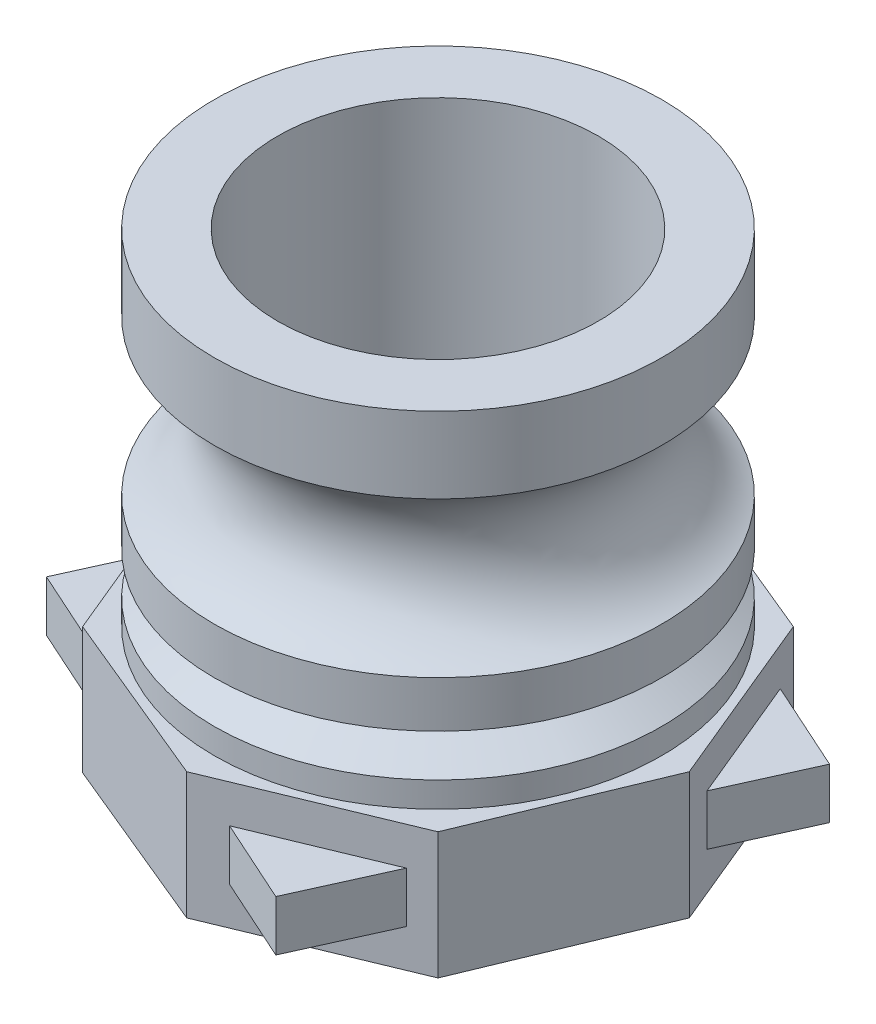
SolidWorks part; units mm, degrees
material "AISI 1020"
ref_plane "Front Plane" through (0, 0, 0) normal (0, 0, 1) x (1, 0, 0)
ref_plane "Top Plane" through (0, 0, 0) normal (0, 1, 0) x (1, 0, 0)
ref_plane "Right Plane" through (0, 0, 0) normal (1, 0, 0) x (0, 0, -1)
sketch "Sketch1" plane through (0, 0, 0) normal (0, 1, 0) x (1, 0, 0)
  line L1 (21.0476, 21.0476) -> (0, 29.7658)
  line L2 (0, 29.7658) -> (-21.0476, 21.0476)
  line L3 (-21.0476, 21.0476) -> (-29.7658, 0)
  line L4 (-29.7658, 0) -> (-21.0476, -21.0476)
  line L5 (-21.0476, -21.0476) -> (0, -29.7658)
  line L6 (0, -29.7658) -> (21.0476, -21.0476)
  line L7 (21.0476, -21.0476) -> (29.7658, 0)
  line L8 (29.7658, 0) -> (21.0476, 21.0476)
  circle A0 centre (0, 0) radius 27.5 construction
  circle A1 centre (0, 0) radius 19
  dimension "D2" = 38
  dimension "D1" = 55
extrude "Boss-Extrude2" add sketch "Sketch1" along normal blind 15
sketch "Sketch2" plane through (0, 0, 0) normal (0, 0, 1) x (1, 0, 0)
  line L0 (0, 102.2518) -> (0, -142.8163) construction
  line L2 (0, 15) -> (21.0476, 15) construction
  line L3 (26.5, 46.8303) -> (26.5, 55.8303)
  line L4 (26.5, 55.8303) -> (0, 55.8303)
  line L5 (0, 55.8303) -> (0, 15)
  line L6 (0, 15) -> (26.5, 15)
  line L10 (26.5, 15) -> (26.5, 28.5)
  arc A0 (26.5, 28.5) -> (26.5, 46.8303) centre (30.5, 37.6652) cw
  point P17 (20.5, 37.6652)
  dimension "D2" = 10
  dimension "D1" = 9
  dimension "D3" = 13.5
  dimension "D4" = 53
  dimension "D5" = 6
revolve "Revolve2" add sketch "Sketch2" angle 360 about L0
sketch "Sketch3" plane through (0, 55.8303, 0) normal (0, 1, 0) x (1, 0, 0)
  circle A0 centre (0, 0) radius 19
  dimension "D1" = 38
extrude "Cut-Extrude1" cut sketch "Sketch3" against normal through all
ref_plane "Plane1" through (0, 7.5, 0) normal (0, 1, 0) x (1, 0, 0)
sketch "Sketch4" plane through (0, 7.5, 0) normal (0, 1, 0) x (1, 0, 0)
  line L0 (22.1456, 18.3968) -> (28.2807, 3.5853)
  line L1 (29.7658, 0) -> (21.0476, 21.0476) construction
  line L2 (28.2807, 3.5853) -> (32.7977, 13.5853)
  line L3 (32.7977, 13.5853) -> (22.1456, 18.3968)
  line L5 (-33.721, 0) -> (96.1184, 0) construction
  line L6 (33.2597, 13.7766) -> (-0.2408, -0.0997) construction
  point P26 (0, 0)
  dimension "D1" = 8
  dimension "D2" = 10
  dimension "D3" = 22.5
  dimension "D4" = 90
extrude "Boss-Extrude3" add sketch "Sketch4" along normal mid plane 6
sketch "Sketch6" plane through (0, 0, 0) normal (0, 0, 1) x (1, 0, 0)
  line L0 (26.5, 23) -> (22.1699, 20.5)
  line L1 (22.1699, 20.5) -> (26.5, 18)
  line L2 (26.5, 18) -> (26.5, 23)
  line L4 (21.0476, 15) -> (29.7658, 15) construction
  line L5 (26.5, 15) -> (26.5, 28.5) construction
  line L6 (0, -19.9543) -> (0, 81.8157) construction
  dimension "D1" = 5
  dimension "D2" = 5
  dimension "D3" = 3
revolve "Cut-Revolve1" cut sketch "Sketch6" angle 360 about L6
pattern_circular "CirPattern1" count 4 every 90 about axis through (0, 0, 0) along (0, 1, 0) of "Boss-Extrude3"
equation "\"A\"= 55"
equation "\"B\"= 38"
equation "\"C\"= 10"
equation "\"D1@Sketch1\"=\"A\""
equation "\"D2@Sketch1\"=\"B\""
equation "\"D2@Sketch2\"=\"C\""
equation "\"D1@Sketch3\"=\"B\""
